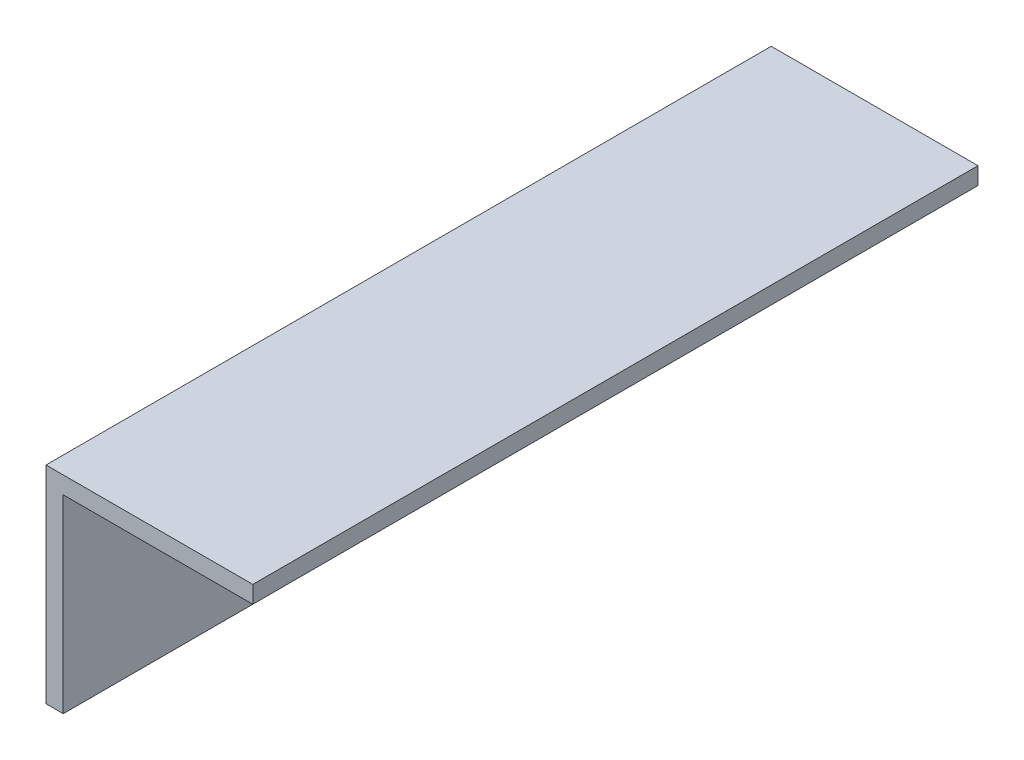
SolidWorks part; units mm, degrees
material "6061-T6 (SS)"
ref_plane "Front Plane" through (0, 0, 0) normal (0, 0, 1) x (1, 0, 0)
ref_plane "Top Plane" through (0, 0, 0) normal (0, 1, 0) x (1, 0, 0)
ref_plane "Right Plane" through (0, 0, 0) normal (1, 0, 0) x (0, 0, -1)
sketch "Sketch1" plane through (0, 0, 0) normal (0, 0, 1) x (1, 0, 0)
  line L0 (0, 0) -> (0, 19.05)
  line L1 (0, 19.05) -> (19.05, 19.05)
  line L2 (19.05, 19.05) -> (19.05, 17.4625)
  line L3 (19.05, 17.4625) -> (1.5875, 17.4625)
  line L4 (1.5875, 17.4625) -> (1.5875, 0)
  line L5 (1.5875, 0) -> (0, 0)
  dimension "D1" = 1.5875
  dimension "D2" = 19.05
extrude "Boss-Extrude2" add sketch "Sketch1" along normal blind 66.802 contours L3 L4 L5 L0 L1 L2
